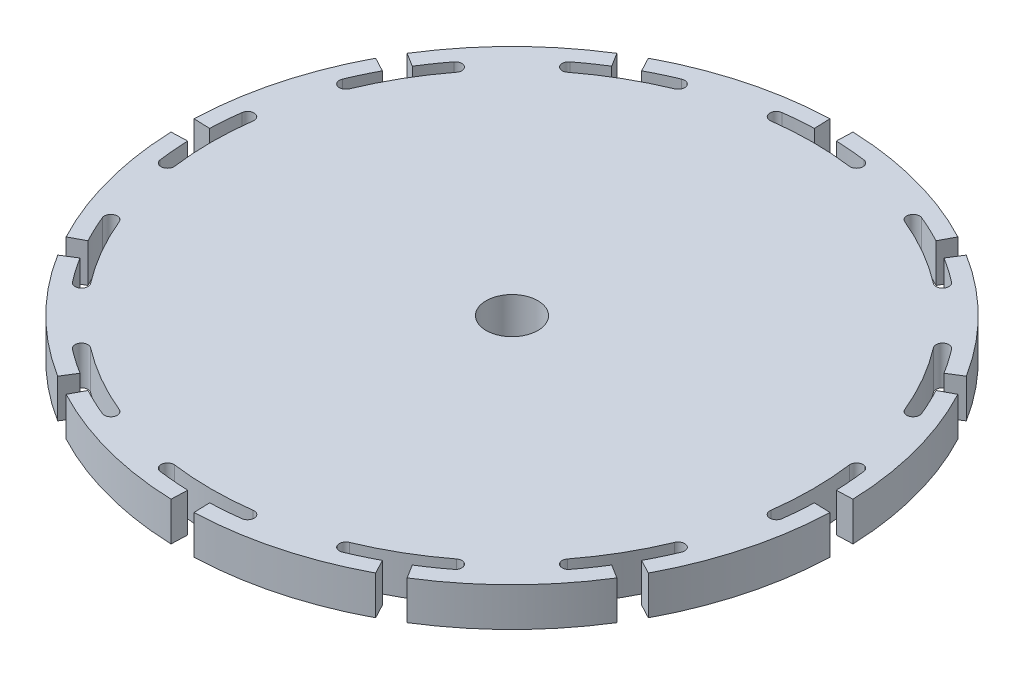
SolidWorks part; units mm, degrees
ref_plane "Front Plane" through (0, 0, 0) normal (0, 0, 1) x (1, 0, 0)
ref_plane "Top Plane" through (0, 0, 0) normal (0, 1, 0) x (1, 0, 0)
ref_plane "Right Plane" through (0, 0, 0) normal (1, 0, 0) x (0, 0, -1)
sketch "Sketch1" plane through (0, 0, 0) normal (0, 1, 0) x (1, 0, 0)
  circle A0 centre (0, 0) radius 51
  dimension "D1" = 102
sketch "Sketch2" plane through (0, 0, 0) normal (0, 1, 0) x (1, 0, 0)
  line L0 (0, 0) -> (0, 51) construction
  line L1 (-1.7799, 50.9689) -> (0, 0) construction
  line L2 (0, 0) -> (-6.6568, 50.5637) construction
  line L3 (-1.7799, 50.9689) -> (-1.6926, 48.4705)
  line L4 (0, 0) -> (6.6568, 50.5637) construction
  line L5 (1.7799, 50.9689) -> (0, 0) construction
  line L6 (1.7799, 50.9689) -> (1.6926, 48.4705)
  line L7 (23.943, 45.0303) -> (22.7694, 42.823)
  line L8 (27.0259, 43.2505) -> (25.7011, 41.1303)
  line L9 (43.2505, 27.0259) -> (41.1303, 25.7011)
  line L10 (45.0303, 23.943) -> (42.823, 22.7694)
  line L11 (50.9689, 1.7799) -> (48.4705, 1.6926)
  line L12 (50.9689, -1.7799) -> (48.4705, -1.6926)
  line L13 (45.0303, -23.943) -> (42.823, -22.7694)
  line L14 (43.2505, -27.0259) -> (41.1303, -25.7011)
  line L15 (27.0259, -43.2505) -> (25.7011, -41.1303)
  line L16 (23.943, -45.0303) -> (22.7694, -42.823)
  line L17 (1.7799, -50.9689) -> (1.6926, -48.4705)
  line L18 (-1.7799, -50.9689) -> (-1.6926, -48.4705)
  line L19 (-23.943, -45.0303) -> (-22.7694, -42.823)
  line L20 (-27.0259, -43.2505) -> (-25.7011, -41.1303)
  line L21 (-43.2505, -27.0259) -> (-41.1303, -25.7011)
  line L22 (-45.0303, -23.943) -> (-42.823, -22.7694)
  line L23 (-50.9689, -1.7799) -> (-48.4705, -1.6926)
  line L24 (-50.9689, 1.7799) -> (-48.4705, 1.6926)
  line L25 (-45.0303, 23.943) -> (-42.823, 22.7694)
  line L26 (-43.2505, 27.0259) -> (-41.1303, 25.7011)
  line L27 (-27.0259, 43.2505) -> (-25.7011, 41.1303)
  line L28 (-23.943, 45.0303) -> (-22.7694, 42.823)
  arc A0 (6.0695, 46.1022) -> (-6.0695, 46.1022) centre (0, 0) ccw
  circle A1 centre (0, 0) radius 51 construction
  arc A2 (-1.7799, 50.9689) -> (1.7799, 50.9689) centre (0, 0) cw
  arc A3 (-1.6926, 48.4705) -> (-6.3305, 48.0851) centre (0, 0) ccw
  arc A4 (-6.0695, 46.1022) -> (-6.3305, 48.0851) centre (-6.2, 47.0936) cw
  arc A5 (6.0695, 46.1022) -> (6.3305, 48.0851) centre (6.2, 47.0936) ccw
  arc A6 (1.6926, 48.4705) -> (6.3305, 48.0851) centre (0, 0) cw
  arc A7 (23.943, 45.0303) -> (27.0259, 43.2505) centre (0, 0) cw
  arc A8 (25.7011, 41.1303) -> (29.5249, 38.4776) centre (0, 0) cw
  arc A9 (28.3074, 36.8909) -> (29.5249, 38.4776) centre (28.9162, 37.6843) ccw
  arc A10 (28.3074, 36.8909) -> (17.7948, 42.9604) centre (0, 0) ccw
  arc A11 (22.7694, 42.823) -> (18.5601, 44.8082) centre (0, 0) ccw
  arc A12 (17.7948, 42.9604) -> (18.5601, 44.8082) centre (18.1775, 43.8843) cw
  arc A13 (43.2505, 27.0259) -> (45.0303, 23.943) centre (0, 0) cw
  arc A14 (42.823, 22.7694) -> (44.8082, 18.5601) centre (0, 0) cw
  arc A15 (42.9604, 17.7948) -> (44.8082, 18.5601) centre (43.8843, 18.1775) ccw
  arc A16 (42.9604, 17.7948) -> (36.8909, 28.3074) centre (0, 0) ccw
  arc A17 (41.1303, 25.7011) -> (38.4776, 29.5249) centre (0, 0) ccw
  arc A18 (36.8909, 28.3074) -> (38.4776, 29.5249) centre (37.6843, 28.9162) cw
  arc A19 (50.9689, 1.7799) -> (50.9689, -1.7799) centre (0, 0) cw
  arc A20 (48.4705, -1.6926) -> (48.0851, -6.3305) centre (0, 0) cw
  arc A21 (46.1022, -6.0695) -> (48.0851, -6.3305) centre (47.0936, -6.2) ccw
  arc A22 (46.1022, -6.0695) -> (46.1022, 6.0695) centre (0, 0) ccw
  arc A23 (48.4705, 1.6926) -> (48.0851, 6.3305) centre (0, 0) ccw
  arc A24 (46.1022, 6.0695) -> (48.0851, 6.3305) centre (47.0936, 6.2) cw
  arc A25 (45.0303, -23.943) -> (43.2505, -27.0259) centre (0, 0) cw
  arc A26 (41.1303, -25.7011) -> (38.4776, -29.5249) centre (0, 0) cw
  arc A27 (36.8909, -28.3074) -> (38.4776, -29.5249) centre (37.6843, -28.9162) ccw
  arc A28 (36.8909, -28.3074) -> (42.9604, -17.7948) centre (0, 0) ccw
  arc A29 (42.823, -22.7694) -> (44.8082, -18.5601) centre (0, 0) ccw
  arc A30 (42.9604, -17.7948) -> (44.8082, -18.5601) centre (43.8843, -18.1775) cw
  arc A31 (27.0259, -43.2505) -> (23.943, -45.0303) centre (0, 0) cw
  arc A32 (22.7694, -42.823) -> (18.5601, -44.8082) centre (0, 0) cw
  arc A33 (17.7948, -42.9604) -> (18.5601, -44.8082) centre (18.1775, -43.8843) ccw
  arc A34 (17.7948, -42.9604) -> (28.3074, -36.8909) centre (0, 0) ccw
  arc A35 (25.7011, -41.1303) -> (29.5249, -38.4776) centre (0, 0) ccw
  arc A36 (28.3074, -36.8909) -> (29.5249, -38.4776) centre (28.9162, -37.6843) cw
  arc A37 (1.7799, -50.9689) -> (-1.7799, -50.9689) centre (0, 0) cw
  arc A38 (-1.6926, -48.4705) -> (-6.3305, -48.0851) centre (0, 0) cw
  arc A39 (-6.0695, -46.1022) -> (-6.3305, -48.0851) centre (-6.2, -47.0936) ccw
  arc A40 (-6.0695, -46.1022) -> (6.0695, -46.1022) centre (0, 0) ccw
  arc A41 (1.6926, -48.4705) -> (6.3305, -48.0851) centre (0, 0) ccw
  arc A42 (6.0695, -46.1022) -> (6.3305, -48.0851) centre (6.2, -47.0936) cw
  arc A43 (-23.943, -45.0303) -> (-27.0259, -43.2505) centre (0, 0) cw
  arc A44 (-25.7011, -41.1303) -> (-29.5249, -38.4776) centre (0, 0) cw
  arc A45 (-28.3074, -36.8909) -> (-29.5249, -38.4776) centre (-28.9162, -37.6843) ccw
  arc A46 (-28.3074, -36.8909) -> (-17.7948, -42.9604) centre (0, 0) ccw
  arc A47 (-22.7694, -42.823) -> (-18.5601, -44.8082) centre (0, 0) ccw
  arc A48 (-17.7948, -42.9604) -> (-18.5601, -44.8082) centre (-18.1775, -43.8843) cw
  arc A49 (-43.2505, -27.0259) -> (-45.0303, -23.943) centre (0, 0) cw
  arc A50 (-42.823, -22.7694) -> (-44.8082, -18.5601) centre (0, 0) cw
  arc A51 (-42.9604, -17.7948) -> (-44.8082, -18.5601) centre (-43.8843, -18.1775) ccw
  arc A52 (-42.9604, -17.7948) -> (-36.8909, -28.3074) centre (0, 0) ccw
  arc A53 (-41.1303, -25.7011) -> (-38.4776, -29.5249) centre (0, 0) ccw
  arc A54 (-36.8909, -28.3074) -> (-38.4776, -29.5249) centre (-37.6843, -28.9162) cw
  arc A55 (-50.9689, -1.7799) -> (-50.9689, 1.7799) centre (0, 0) cw
  arc A56 (-48.4705, 1.6926) -> (-48.0851, 6.3305) centre (0, 0) cw
  arc A57 (-46.1022, 6.0695) -> (-48.0851, 6.3305) centre (-47.0936, 6.2) ccw
  arc A58 (-46.1022, 6.0695) -> (-46.1022, -6.0695) centre (0, 0) ccw
  arc A59 (-48.4705, -1.6926) -> (-48.0851, -6.3305) centre (0, 0) ccw
  arc A60 (-46.1022, -6.0695) -> (-48.0851, -6.3305) centre (-47.0936, -6.2) cw
  arc A61 (-45.0303, 23.943) -> (-43.2505, 27.0259) centre (0, 0) cw
  arc A62 (-41.1303, 25.7011) -> (-38.4776, 29.5249) centre (0, 0) cw
  arc A63 (-36.8909, 28.3074) -> (-38.4776, 29.5249) centre (-37.6843, 28.9162) ccw
  arc A64 (-36.8909, 28.3074) -> (-42.9604, 17.7948) centre (0, 0) ccw
  arc A65 (-42.823, 22.7694) -> (-44.8082, 18.5601) centre (0, 0) ccw
  arc A66 (-42.9604, 17.7948) -> (-44.8082, 18.5601) centre (-43.8843, 18.1775) cw
  arc A67 (-27.0259, 43.2505) -> (-23.943, 45.0303) centre (0, 0) cw
  arc A68 (-22.7694, 42.823) -> (-18.5601, 44.8082) centre (0, 0) cw
  arc A69 (-17.7948, 42.9604) -> (-18.5601, 44.8082) centre (-18.1775, 43.8843) ccw
  arc A70 (-17.7948, 42.9604) -> (-28.3074, 36.8909) centre (0, 0) ccw
  arc A71 (-25.7011, 41.1303) -> (-29.5249, 38.4776) centre (0, 0) ccw
  arc A72 (-28.3074, 36.8909) -> (-29.5249, 38.4776) centre (-28.9162, 37.6843) cw
  point P130 (0, 0)
  dimension "D1" = 15
  dimension "D5" = 12
  dimension "D2" = 2
  dimension "D4" = 2.5
  dimension "D3" = 4
sketch "Sketch3" plane through (0, 0, 0) normal (0, 1, 0) x (1, 0, 0)
  circle A0 centre (0, 0) radius 4
  dimension "D1" = 8
extrude "Boss-Extrude1" add sketch "Sketch1" along normal blind 6
extrude "Cut-Extrude1" cut sketch "Sketch2" along normal through all
extrude "Cut-Extrude2" cut sketch "Sketch3" along normal blind 6
